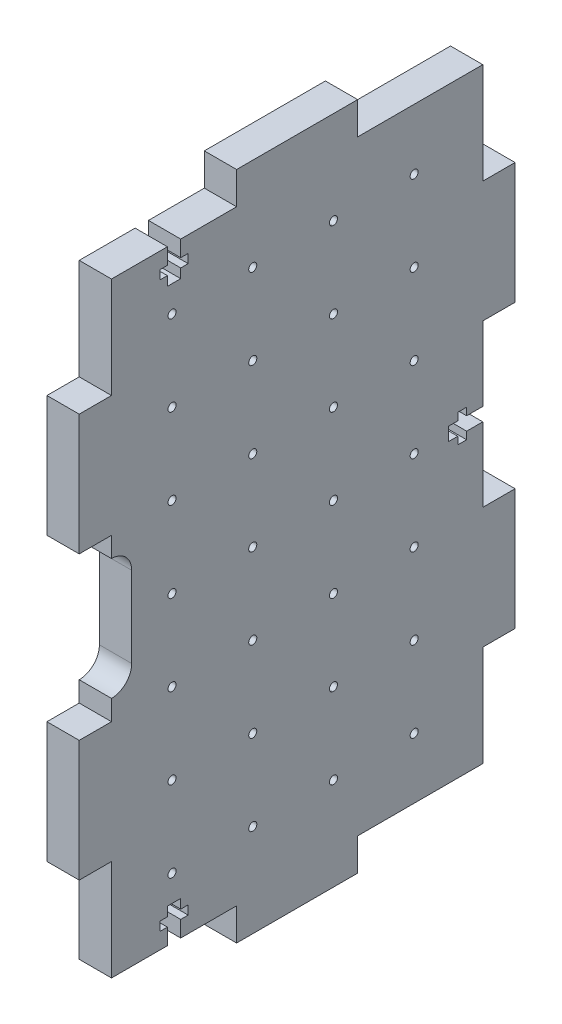
SolidWorks part; units mm, degrees
material "Acrylic (Medium-high impact)"
ref_plane "Front Plane" through (0, 0, 0) normal (0, 0, 1) x (1, 0, 0)
ref_plane "Top Plane" through (0, 0, 0) normal (0, 1, 0) x (1, 0, 0)
ref_plane "Right Plane" through (0, 0, 0) normal (1, 0, 0) x (0, 0, -1)
sketch "Sketch1" plane through (0, 0, 0) normal (1, 0, 0) x (0, 0, -1)
  line L1 (0, 0) -> (92, 0)
  line L2 (0, 0) -> (0, 150)
  line L3 (0, 150) -> (92, 150)
  line L4 (92, 0) -> (92, 150)
  dimension "D1" = 92
  dimension "D2" = 150
extrude "Boss-Extrude1" add sketch "Sketch1" along normal blind 8
sketch "Sketch2" plane through (0, 0, 0) normal (-1, 0, 0) x (0, 0, 1)
  line L0 (-92, 150) -> (0, 150) construction
  line L1 (-61, 150) -> (-31, 150)
  line L2 (-61, 150) -> (-61, 158)
  line L3 (-61, 158) -> (-31, 158)
  line L4 (-31, 150) -> (-31, 158)
  line L5 (-46, 150) -> (-46, 0) construction
  line L6 (0, 0) -> (-92, 0) construction
  line L7 (-92, 75) -> (0, 75) construction
  line L8 (-92, 0) -> (-92, 150) construction
  line L9 (0, 150) -> (0, 0) construction
  line L10 (-31, 0) -> (-31, -8)
  line L11 (-61, -8) -> (-31, -8)
  line L12 (-61, 0) -> (-61, -8)
  line L13 (-61, 0) -> (-31, 0)
  line L14 (8, 25) -> (8, 55)
  line L15 (0, 125) -> (8, 125)
  line L16 (0, 125) -> (0, 95)
  line L17 (0, 95) -> (8, 95)
  line L18 (8, 125) -> (8, 95)
  line L19 (0, 55) -> (8, 55)
  line L20 (0, 25) -> (0, 55)
  line L21 (0, 25) -> (8, 25)
  line L22 (-92, 25) -> (-100, 25)
  line L23 (-92, 25) -> (-92, 55)
  line L24 (-92, 55) -> (-100, 55)
  line L25 (-100, 125) -> (-100, 95)
  line L26 (-92, 95) -> (-100, 95)
  line L27 (-92, 125) -> (-92, 95)
  line L28 (-92, 125) -> (-100, 125)
  line L29 (-100, 25) -> (-100, 55)
  point P6 (-46, 158)
  point P21 (-46, -8)
  point P26 (8, 110)
  point P33 (8, 40)
  point P42 (-100, 40)
  point P43 (-100, 110)
  dimension "D1" = 30
  dimension "D2" = 8
  dimension "D3" = 30
  dimension "D4" = 8
  dimension "D5" = 25
extrude "Boss-Extrude2" add sketch "Sketch2" against normal blind 8
sketch "Sketch3" plane through (8, 0, 0) normal (1, 0, 0) x (0, 0, -1)
  line L0 (31, 150) -> (0, 150) construction
  line L1 (0, 150) -> (0, 125) construction
  circle A0 centre (15, 135) radius 1
  circle A1 centre (35, 135) radius 1
  circle A2 centre (55, 135) radius 1
  circle A3 centre (75, 135) radius 1
  circle A4 centre (15, 115) radius 1
  circle A5 centre (35, 115) radius 1
  circle A6 centre (55, 115) radius 1
  circle A7 centre (75, 115) radius 1
  circle A8 centre (15, 95) radius 1
  circle A9 centre (35, 95) radius 1
  circle A10 centre (55, 95) radius 1
  circle A11 centre (75, 95) radius 1
  circle A12 centre (15, 75) radius 1
  circle A13 centre (35, 75) radius 1
  circle A14 centre (55, 75) radius 1
  circle A15 centre (75, 75) radius 1
  circle A16 centre (15, 55) radius 1
  circle A17 centre (35, 55) radius 1
  circle A18 centre (55, 55) radius 1
  circle A19 centre (75, 55) radius 1
  circle A20 centre (15, 35) radius 1
  circle A21 centre (35, 35) radius 1
  circle A22 centre (55, 35) radius 1
  circle A23 centre (75, 35) radius 1
  circle A24 centre (15, 15) radius 1
  circle A25 centre (35, 15) radius 1
  circle A26 centre (55, 15) radius 1
  circle A27 centre (75, 15) radius 1
  dimension "D1" = 2
  dimension "D4" = 15
  dimension "D5" = 15
  dimension "D2" = 4
extrude "Cut-Extrude1" cut sketch "Sketch3" against normal blind 8
sketch "Sketch4" plane through (8, 0, 0) normal (1, 0, 0) x (0, 0, -1)
  line L0 (0, 85) -> (0, 65) construction
  line L2 (5, 85) -> (5, 65)
  line L3 (-5, 85) -> (-5, 65)
  line L4 (0, 95) -> (0, 55) construction
  arc A0 (5, 85) -> (-5, 85) centre (0, 85) ccw
  arc A1 (-5, 65) -> (5, 65) centre (0, 65) ccw
  point P4 (0, 75)
  dimension "D2" = 5
  dimension "D1" = 20
extrude "Cut-Extrude2" cut sketch "Sketch4" against normal through all
sketch "Sketch5" plane through (8, 0, 0) normal (1, 0, 0) x (0, 0, -1)
  line L0 (92, 75) -> (5, 75) construction
  line L1 (92, 55) -> (92, 95) construction
  line L2 (5, 65) -> (5, 85) construction
  line L3 (92, 76.65) -> (88, 76.65)
  line L4 (88, 76.65) -> (88, 78.5)
  line L5 (88, 78.5) -> (85.8, 78.5)
  line L6 (85.8, 78.5) -> (85.8, 76.65)
  line L7 (85.8, 76.65) -> (83.5, 76.65)
  line L8 (83.5, 76.65) -> (83.5, 73.35)
  line L9 (85.8, 73.35) -> (83.5, 73.35)
  line L10 (85.8, 71.5) -> (85.8, 73.35)
  line L11 (88, 71.5) -> (85.8, 71.5)
  line L12 (88, 73.35) -> (88, 71.5)
  line L13 (92, 73.35) -> (88, 73.35)
  line L14 (92, 76.65) -> (92, 73.35)
  line L15 (15.5, 0) -> (15.5, 158.5355) construction
  line L16 (17.15, 0) -> (17.15, 4)
  line L17 (17.15, 4) -> (19, 4)
  line L18 (19, 4) -> (19, 6.2)
  line L19 (19, 6.2) -> (17.15, 6.2)
  line L20 (17.15, 6.2) -> (17.15, 8.5)
  line L21 (17.15, 8.5) -> (13.85, 8.5)
  line L22 (13.85, 6.2) -> (13.85, 8.5)
  line L23 (12, 6.2) -> (13.85, 6.2)
  line L24 (12, 4) -> (12, 6.2)
  line L25 (13.85, 4) -> (12, 4)
  line L26 (13.85, 0) -> (13.85, 4)
  line L27 (13.85, 0) -> (17.15, 0)
  line L28 (13.85, 150) -> (17.15, 150)
  line L29 (13.85, 150) -> (13.85, 146)
  line L30 (13.85, 146) -> (12, 146)
  line L31 (12, 146) -> (12, 143.8)
  line L32 (12, 143.8) -> (13.85, 143.8)
  line L33 (13.85, 143.8) -> (13.85, 141.5)
  line L34 (17.15, 141.5) -> (13.85, 141.5)
  line L35 (17.15, 143.8) -> (17.15, 141.5)
  line L36 (19, 143.8) -> (17.15, 143.8)
  line L37 (19, 146) -> (19, 143.8)
  line L38 (17.15, 146) -> (19, 146)
  line L39 (17.15, 150) -> (17.15, 146)
  line L40 (0, 0) -> (31, 0) construction
  point P14 (83.5, 75)
  point P29 (15.5, 8.5)
  point P46 (15.5, 141.5)
  dimension "D1" = 3.3
  dimension "D2" = 7
  dimension "D3" = 4
  dimension "D4" = 2.2
  dimension "D5" = 2.3
  dimension "D6" = 7
  dimension "D7" = 4
  dimension "D8" = 2.2
  dimension "D9" = 2.3
  dimension "D10" = 3.3
extrude "Cut-Extrude4" cut sketch "Sketch5" against normal through all
